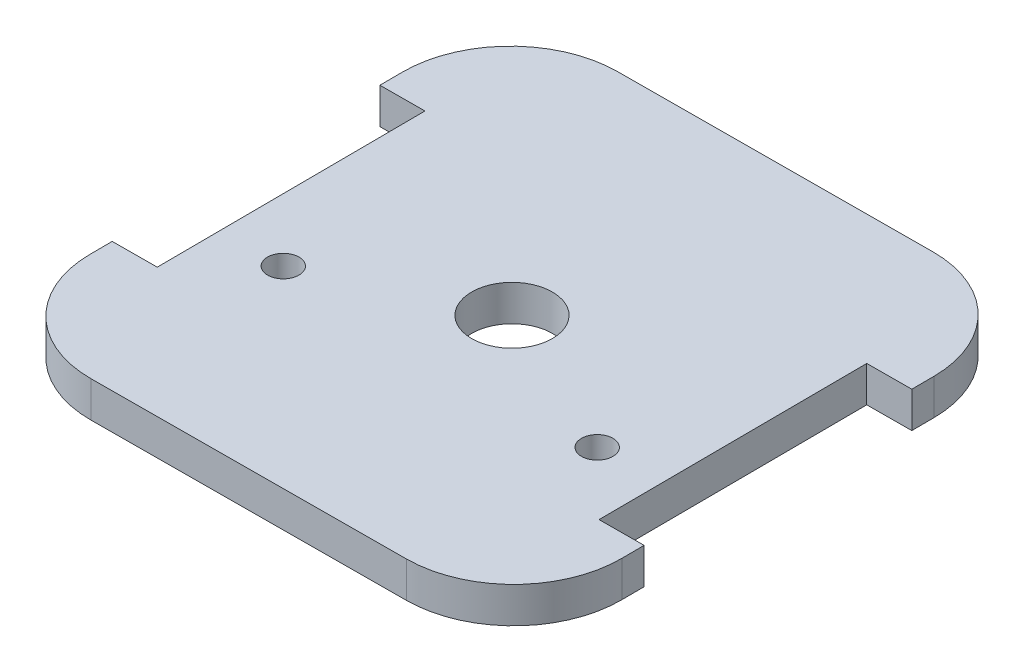
SolidWorks part; units mm, degrees
ref_plane "Front Plane" through (0, 0, 0) normal (0, 0, 1) x (1, 0, 0)
ref_plane "Top Plane" through (0, 0, 0) normal (0, 1, 0) x (1, 0, 0)
ref_plane "Right Plane" through (0, 0, 0) normal (1, 0, 0) x (0, 0, -1)
sketch "Sketch1" plane through (0, 0, 0) normal (0, 1, 0) x (1, 0, 0)
  line L0 (29.1807, -16.12) -> (29.0904, 1.3797)
  line L1 (29.0904, 1.3797) -> (29.0001, 18.8795)
  line L2 (16.9384, 30.8174) -> (-18.0611, 30.6369)
  line L3 (-29.9991, 18.5752) -> (-29.8185, -16.4244)
  line L4 (-17.7568, -28.3623) -> (17.2428, -28.1818)
  line L5 (-0.5614, 30.7272) -> (-0.257, -28.272) construction
  arc A0 (29.0001, 18.8795) -> (16.9384, 30.8174) centre (17.0003, 18.8176) ccw
  arc A1 (-18.0611, 30.6369) -> (-29.9991, 18.5752) centre (-17.9992, 18.6371) ccw
  arc A2 (-29.8185, -16.4244) -> (-17.7568, -28.3623) centre (-17.8187, -16.3625) ccw
  arc A3 (17.2428, -28.1818) -> (29.1807, -16.12) centre (17.1809, -16.1819) ccw
  arc A4 (17.0908, -8.5224) -> (17.0908, -5.0224) centre (17.0908, -6.7724) ccw
  arc A5 (17.0908, -5.0224) -> (17.0908, -8.5224) centre (17.0908, -6.7724) ccw
  arc A6 (-17.9092, -5.0224) -> (-17.9092, -8.5224) centre (-17.9092, -6.7724) ccw
  arc A7 (-17.9092, -8.5224) -> (-17.9092, -5.0224) centre (-17.9092, -6.7724) ccw
  arc A8 (-0.4092, 5.7276) -> (-0.4092, -3.2724) centre (-0.4092, 1.2276) ccw
  arc A9 (-0.4092, -3.2724) -> (-0.4092, 5.7276) centre (-0.4092, 1.2276) ccw
  point P28 (-0.4092, 1.2276)
  dimension "D1" = 59
  dimension "D2" = 59
extrude "Boss-Extrude1" add sketch "Sketch1" along normal blind 4
sketch "Sketch2" plane through (0, 4, 0) normal (0, 1, 0) x (1, 0, 0)
  line L0 (29.013, 16.3797) -> (29.1678, -13.6203)
  line L2 (29.1807, -16.12) -> (29.0001, 18.8795) construction
  line L3 (29.013, 16.3797) -> (29.1678, -13.6203)
  line L4 (29.013, 16.3797) -> (24.0131, 16.3539)
  line L5 (29.1678, -13.6203) -> (24.1679, -13.6461)
  line L6 (24.0131, 16.3539) -> (24.1679, -13.6461)
  line L7 (-0.5614, 30.7272) -> (-0.257, -28.272) construction
  line L8 (16.9384, 30.8174) -> (-18.0611, 30.6369) construction
  line L9 (-17.7568, -28.3623) -> (17.2428, -28.1818) construction
  line L10 (-24.9862, 16.1012) -> (-24.8315, -13.8988)
  line L11 (-29.8314, -13.9246) -> (-24.8315, -13.8988)
  line L12 (-29.9862, 16.0754) -> (-24.9862, 16.1012)
  line L13 (-29.9862, 16.0754) -> (-29.8314, -13.9246)
  line L14 (-29.9862, 16.0754) -> (-29.8314, -13.9246)
  point P0 (29.0904, 1.3797)
  point P5 (29.0904, 1.3797)
  point P18 (-29.9088, 1.0754)
  line M6 (29.1807, -16.12) -> (29.0001, 18.8795)
  line M10 (-29.9991, 18.5752) -> (-29.8185, -16.4244)
  dimension "D1" = 30
  dimension "D2" = 5
extrude "Cut-Extrude2" cut sketch "Sketch2" against normal blind 32 contours L12 L11 L10 M10 | L4 L6 L5 M6
